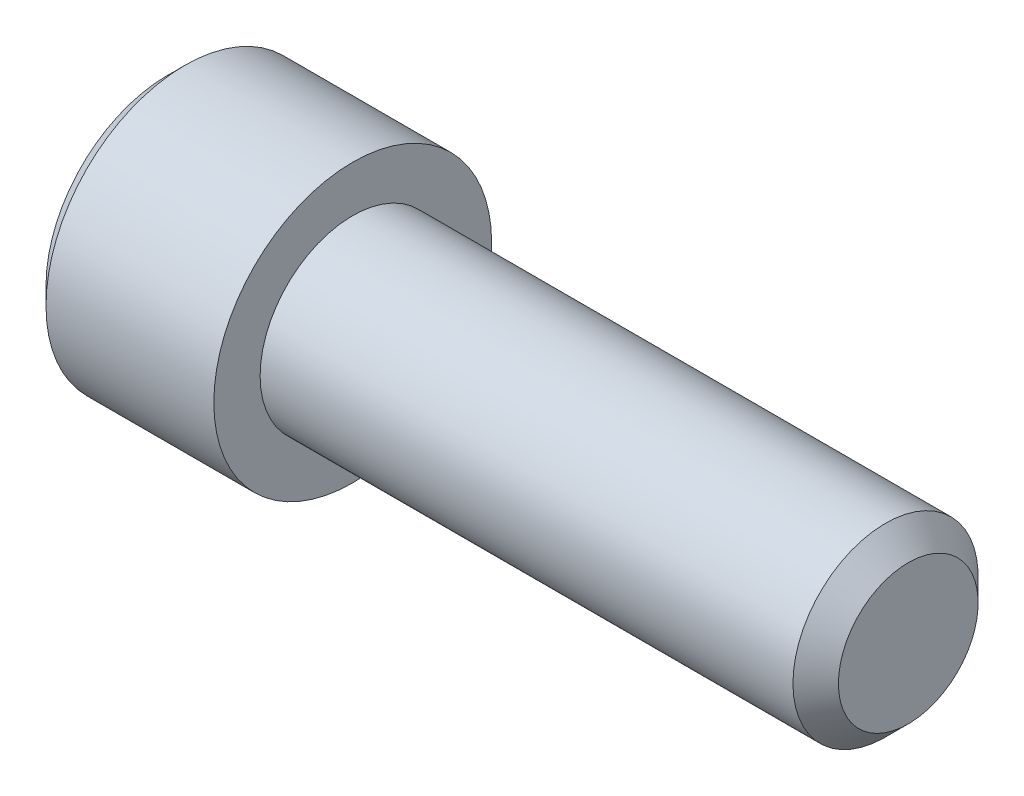
SolidWorks part; units mm, degrees
material "AISI 304"
ref_plane "正面" through (0, 0, 0) normal (0, 0, 1) x (1, 0, 0)
ref_plane "平面" through (0, 0, 0) normal (0, 1, 0) x (1, 0, 0)
ref_plane "右側面" through (0, 0, 0) normal (1, 0, 0) x (0, 0, -1)
ref_plane "Plane1" through (0, 0, 0) normal (0, 0, 1) x (1, 0, 0)
sketch "Sketch1" plane through (0, 0, 0) normal (0, 0, 1) x (1, 0, 0)
  line L0 (-2, 0) -> (-2, 1.3125)
  line L1 (-2, 1.3125) -> (-1.8125, 1.5)
  line L2 (-1.8125, 1.5) -> (0, 1.5)
  line L3 (0, 1.5) -> (0, 1)
  line L4 (0, 1) -> (5.7545, 1)
  line L5 (5.7545, 1) -> (6, 0.7545)
  line L6 (6, 0.7545) -> (6, 0)
  line L7 (6, 0) -> (-2, 0)
  line L8 (6, 0) -> (-2, 0) construction
revolve "Revolve1" add sketch "Sketch1" angle 360 about L8
cosmetic thread "Cosmetic Thread1" parameters "D1"=5.5, "D2"=1.509
ref_plane "Plane2" through (0, 0, 0) normal (0, 0, 1) x (1, 0, 0)
sketch "Sketch2" plane through (0, 0, 0) normal (0, 0, 1) x (1, 0, 0)
  line L0 (-2, 0) -> (-2, 0.9)
  line L1 (-2, 0.9) -> (-1.85, 0.75)
  line L2 (-1.85, 0.75) -> (-1, 0.75)
  line L3 (-1, 0.75) -> (-0.6, 0)
  line L4 (-0.6, 0) -> (-2, 0)
  line L5 (-0.6, 0) -> (-2, 0) construction
revolve "Cut-Revolve1" cut sketch "Sketch2" angle 360 about L5
ref_plane "Plane3" through (-2, 0, 0) normal (1, 0, 0) x (0, 0, -1)
sketch "Sketch3" plane through (-2, 0, 0) normal (1, 0, 0) x (0, 0, -1)
  line L0 (-0.75, -0.433) -> (0, -0.866)
  line L1 (0, -0.866) -> (0.75, -0.433)
  line L2 (0.75, -0.433) -> (0.75, 0.433)
  line L3 (0.75, 0.433) -> (0, 0.866)
  line L4 (0, 0.866) -> (-0.75, 0.433)
  line L5 (-0.75, 0.433) -> (-0.75, -0.433)
extrude "Cut-Extrude1" cut sketch "Sketch3" along normal blind 1
